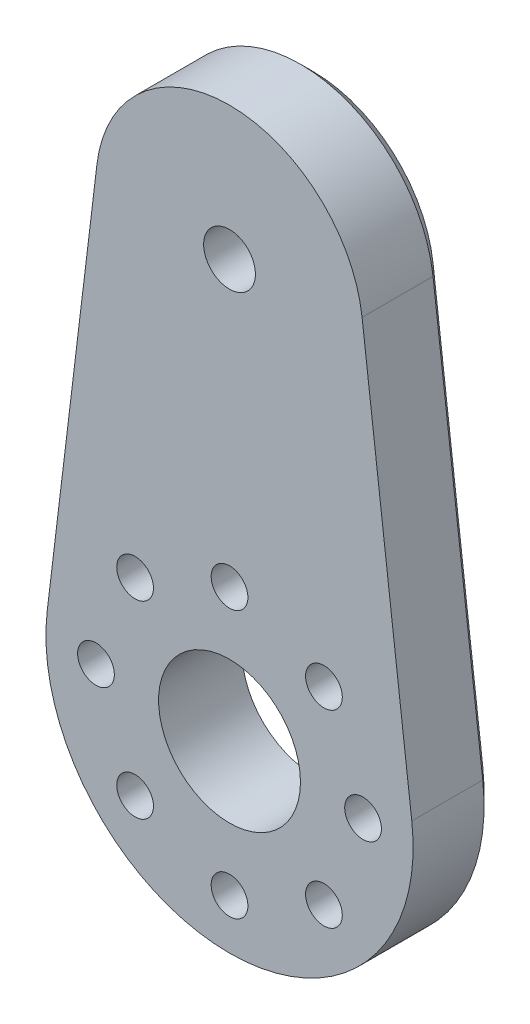
SolidWorks part; units mm, degrees
ref_plane "Front Plane" through (0, 0, 0) normal (0, 0, 1) x (1, 0, 0)
ref_plane "Top Plane" through (0, 0, 0) normal (0, 1, 0) x (1, 0, 0)
ref_plane "Right Plane" through (0, 0, 0) normal (1, 0, 0) x (0, 0, -1)
sketch "Sketch1" plane through (0, 0, 0) normal (0, 0, 1) x (1, 0, 0)
  line L0 (-23.0208, 6.2161) -> (-25.9991, -18.4239)
  line L3 (-7.1364, 6.2161) -> (-4.1581, -18.4239)
  line L4 (-15.0786, 0.8298) -> (-15.0786, 20.8298) construction
  line L5 (-14.7274, -19.7439) -> (49985.2726, -19.7439) construction
  circle A2 centre (-15.0786, 5.2561) radius 1.55
  circle A3 centre (-15.0786, -19.7439) radius 4.25
  arc A5 (-7.1364, 6.2161) -> (-23.0208, 6.2161) centre (-15.0786, 5.2561) ccw
  arc A6 (-25.9991, -18.4239) -> (-4.1581, -18.4239) centre (-15.0786, -19.7439) ccw
  circle A7 centre (-15.0314, -20.0888) radius 11 construction
  circle A8 centre (-7.0786, -19.7439) radius 1.1
  circle A9 centre (-9.4218, -25.4008) radius 1.1
  circle A10 centre (-15.0786, -27.7439) radius 1.1
  circle A11 centre (-20.7355, -25.4008) radius 1.1
  circle A12 centre (-23.0786, -19.7439) radius 1.1
  circle A13 centre (-20.7355, -14.087) radius 1.1
  circle A14 centre (-15.0786, -11.7439) radius 1.1
  circle A15 centre (-9.4218, -14.087) radius 1.1
  point P30 (-15.0786, -19.7439)
  dimension "D1" = 3.1
  dimension "D3" = 25
  dimension "D4" = 11
  dimension "D2" = 8
  dimension "D5" = 8.5
  dimension "D6" = 2.2
  dimension "D7" = 8
  dimension "D8" = 8
extrude "Boss-Extrude1" add sketch "Sketch1" along normal blind 5
sketch "Sketch2" plane through (0, 0, 5) normal (0, 0, 1) x (1, 0, 0)
  circle A0 centre (-15.0786, -19.7439) radius 11.5
  dimension "D1" = 23
extrude "Cut-Extrude1" [suppressed] cut sketch "Sketch2" against normal blind 1.75
sketch "Sketch3" plane through (0, 0, 0) normal (0, 0, 1) x (1, 0, 0)
  line L1 (-13.4909, 2.5061) -> (-11.9032, 5.2561)
  line L2 (-11.9032, 5.2561) -> (-13.4909, 8.0061)
  line L3 (-13.4909, 8.0061) -> (-16.6663, 8.0061)
  line L4 (-16.6663, 8.0061) -> (-18.2541, 5.2561)
  line L5 (-18.2541, 5.2561) -> (-16.6663, 2.5061)
  line L6 (-16.6663, 2.5061) -> (-13.4909, 2.5061)
  circle A0 centre (-15.0786, 5.2561) radius 2.75 construction
  dimension "D1" = 5.5
extrude "Cut-Extrude2" cut sketch "Sketch3" along normal blind 2
sketch "Sketch5" plane through (0, 0, 5) normal (0, 0, 1) x (1, 0, 0)
  circle A2 centre (-14.8897, 3.8764) radius 1.55
  circle A3 centre (-14.8897, 3.8764) radius 8
extrude "Boss-Extrude2" [suppressed] add sketch "Sketch5" along normal blind 3
fillet "Fillet1" [suppressed] radius 1
sketch "Sketch4" plane through (0, 0, 0) normal (0, 0, -1) x (-1, 0, 0)
  circle A0 centre (23.0786, -19.7439) radius 1.75
  circle A1 centre (20.7355, -25.4008) radius 1.75
  circle A2 centre (15.0786, -27.7439) radius 1.75
  circle A3 centre (9.4218, -25.4008) radius 1.75
  circle A4 centre (7.0786, -19.7439) radius 1.75
  circle A5 centre (9.4218, -14.087) radius 1.75
  circle A6 centre (15.0786, -11.7439) radius 1.75
  circle A7 centre (20.7355, -14.087) radius 1.75
  circle A10 centre (15.0786, -19.7439) radius 4.25 construction
  point P20 (15.0786, -19.7439)
  dimension "D1" = 3.5
extrude "Cut-Extrude3" cut sketch "Sketch4" against normal blind 2.25
chamfer "Chaflán1" distance 0.75 angle 45 4 edges at (-24.51, -6.1039, 0) (-15.0786, -30.7439, 0) (-15.0786, 13.2561, 0) (-5.6473, -6.1039, 0)
